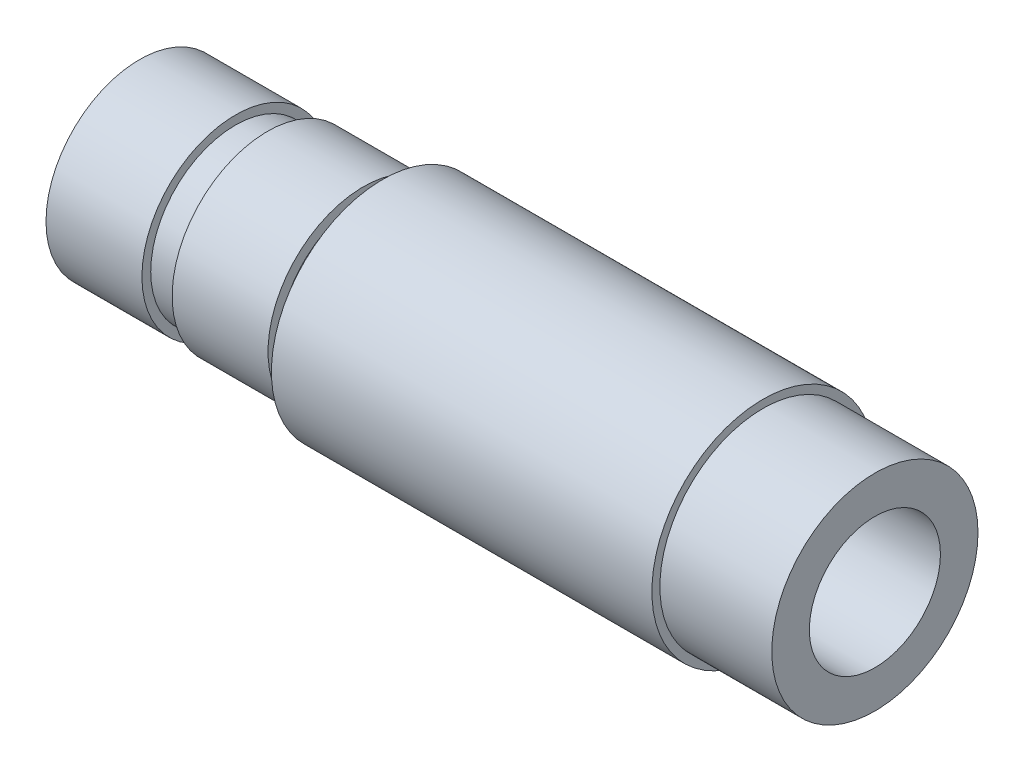
SolidWorks part; units mm, degrees
ref_plane "Front Plane" through (0, 0, 0) normal (0, 0, 1) x (1, 0, 0)
ref_plane "Top Plane" through (0, 0, 0) normal (0, 1, 0) x (1, 0, 0)
ref_plane "Right Plane" through (0, 0, 0) normal (1, 0, 0) x (0, 0, -1)
sketch "Sketch2" plane through (0, 0, 0) normal (0, 0, 1) x (1, 0, 0)
  line L0 (277.539, 63.4078) -> (314.539, 63.3714) construction
  line L1 (307.7622, 76.8439) -> (284.7622, 76.8439)
  line L2 (304.2622, 80.3189) -> (304.2622, 80.0689)
  line L3 (304.2622, 80.0689) -> (307.7622, 80.0689)
  line L6 (307.7622, 76.8439) -> (307.7622, 80.0689)
  line L8 (291.7622, 79.8239) -> (291.7622, 79.4939)
  line L11 (284.7622, 76.8439) -> (284.7622, 79.7689)
  line L12 (284.7622, 79.7689) -> (287.7622, 79.7689)
  line L13 (287.7622, 79.7689) -> (287.7622, 79.4939)
  line L14 (287.7622, 79.4939) -> (288.7622, 79.4939)
  line L15 (288.7622, 79.4939) -> (288.7622, 79.8239)
  line L16 (288.7622, 79.8239) -> (291.7622, 79.8239)
  line L17 (291.7622, 79.4939) -> (292.3622, 79.4939)
  line L18 (292.3622, 79.4939) -> (292.3622, 80.3189)
  line L19 (292.3622, 80.3189) -> (304.2622, 80.3189)
  dimension "D6" = 2.65
  dimension "D1" = 37
  dimension "D2" = 23
  dimension "D3" = 3.5
  dimension "D4" = 3
  dimension "D5" = 1
  dimension "D7" = 2.925
  dimension "D8" = 2.98
  dimension "D9" = 2.65
  dimension "D10" = 3
  dimension "D11" = 3.475
  dimension "D12" = 3.225
revolve "Revolve4" add sketch "Sketch2" angle 360 about L1
hole_wizard "Tap Drill for M5 Tap1" positions "Sketch4" profile "Sketch3" hole size "M5" standard "ISO"
sketch "Sketch4" plane through (307.7622, 0, 0) normal (1, 0, 0) x (0, 0, -1)
  point P0 (0, 76.8439)
sketch "Sketch3" plane through (307.7622, 76.8439, 0) normal (0, 1, 0) x (0, 0, -1)
  line L0 (0, 0) -> (0, 6.7318)
  line L1 (0, 6.7318) -> (2.05, 5.5)
  line L2 (2.05, 5.5) -> (2.05, 0)
  line L5 (2.05, 0) -> (0, 0)
  line L10 (0, 6.7318) -> (-2.05, 5.5) construction
  line L11 (0, -6.35) -> (0, 107.95) construction
  dimension "Hole Dia." = 4.1
  dimension "Hole Depth" = 5.5
  dimension "Drill Angle" = 118
sketch "Sketch5" plane through (284.7622, 0, 0) normal (-1, 0, 0) x (0, 0, 1)
  circle A0 centre (0, 76.8439) radius 1.75
extrude "Cut-Extrude1" cut sketch "Sketch5" against normal blind 29.8
